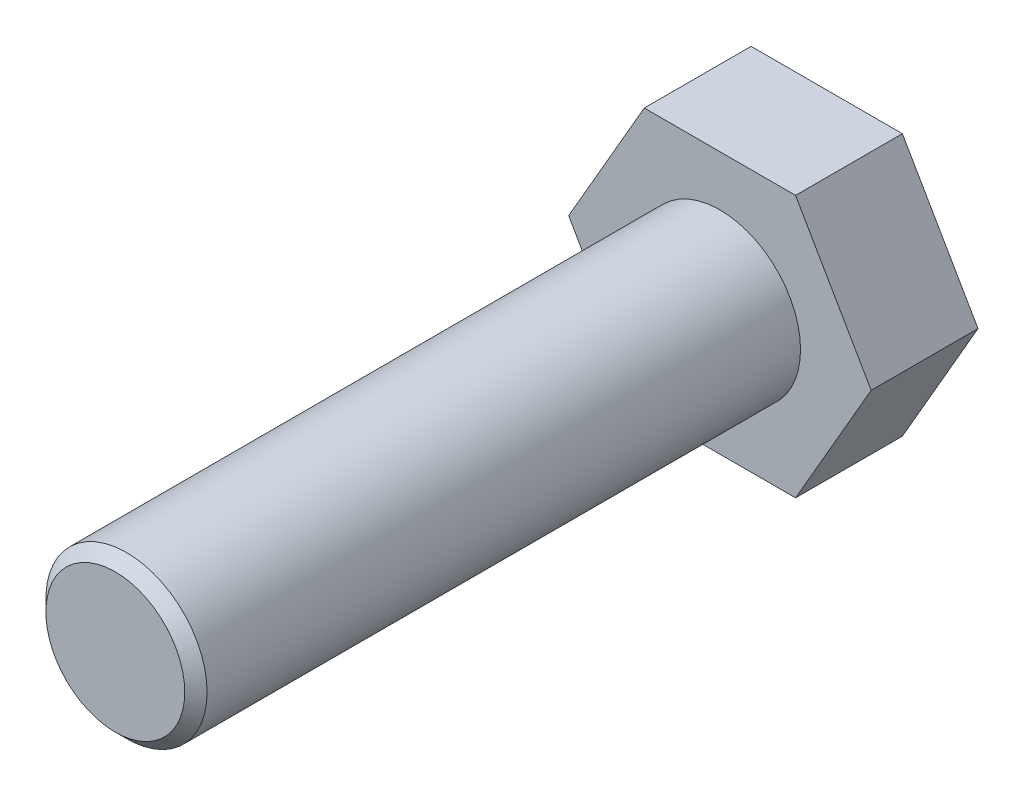
SolidWorks part; units mm, degrees
material "Сталь"
ref_plane "Спереди" through (0, 0, 0) normal (0, 0, 1) x (1, 0, 0)
ref_plane "Сверху" through (0, 0, 0) normal (0, 1, 0) x (1, 0, 0)
ref_plane "Справа" through (0, 0, 0) normal (1, 0, 0) x (0, 0, -1)
sketch "Эскиз1" plane through (0, 0, 0) normal (0, 0, 1) x (1, 0, 0)
  line L1 (3.7528, 6.5) -> (-3.7528, 6.5)
  line L2 (-3.7528, 6.5) -> (-7.5056, 0)
  line L3 (-7.5056, 0) -> (-3.7528, -6.5)
  line L4 (-3.7528, -6.5) -> (3.7528, -6.5)
  line L5 (3.7528, -6.5) -> (7.5056, 0)
  line L6 (7.5056, 0) -> (3.7528, 6.5)
  circle A0 centre (0, 0) radius 6.5 construction
  dimension "D1" = 13
extrude "Бобышка-Вытянуть1" add sketch "Эскиз1" along normal blind 5.3
sketch "Эскиз2" plane through (0, 0, 5.3) normal (0, 0, 1) x (1, 0, 0)
  circle A0 centre (0, 0) radius 4
  dimension "D1" = 8
extrude "Бобышка-Вытянуть2" add sketch "Эскиз2" along normal blind 30
cosmetic thread "Условное изображение резьбы1" parameters "D1"=25, "D2"=6.619
chamfer "Фаска1" distance 0.5545 angle 45 1 edges at (4, 0, 35.3)
